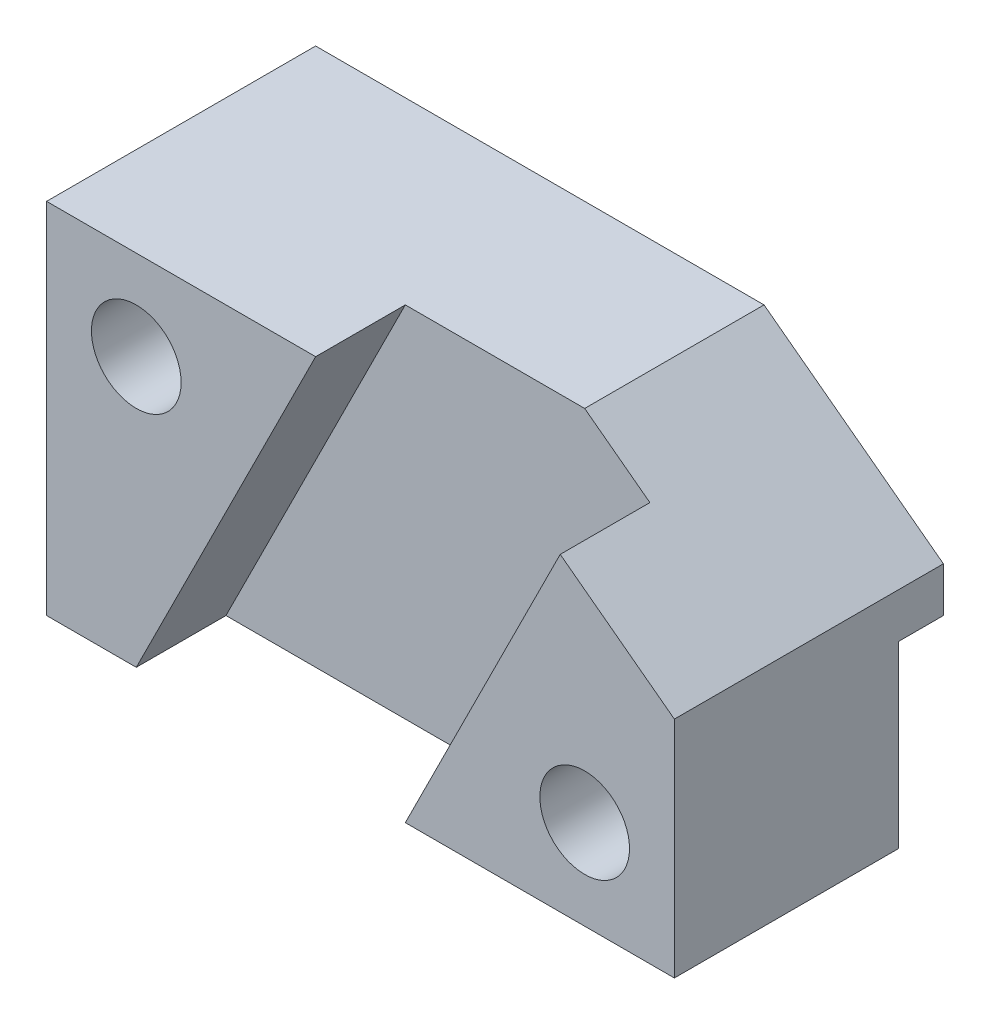
SolidWorks part; units mm, degrees
ref_plane "Front Plane" through (0, 0, 0) normal (0, 0, 1) x (1, 0, 0)
ref_plane "Top Plane" through (0, 0, 0) normal (0, 1, 0) x (1, 0, 0)
ref_plane "Right Plane" through (0, 0, 0) normal (1, 0, 0) x (0, 0, -1)
sketch "Sketch1" plane through (0, 0, 0) normal (0, 1, 0) x (1, 0, 0)
  line L1 (0, 0) -> (70, 0)
  line L2 (0, 0) -> (0, 30)
  line L3 (0, 30) -> (70, 30)
  line L4 (70, 0) -> (70, 30)
  dimension "D1" = 70
  dimension "D2" = 30
extrude "Boss-Extrude1" add sketch "Sketch1" along normal blind 40
sketch "Sketch2" plane through (0, 0, 0) normal (0, 0, 1) x (1, 0, 0)
  line L0 (0, 40) -> (30, 40) construction
  line L1 (0, 40) -> (70, 40) construction
  line L2 (70, 0) -> (40, 0) construction
  line L3 (0, 0) -> (70, 0) construction
  line L4 (70, 40) -> (60, 40) construction
  line L5 (0, 0) -> (10, 0) construction
  line L6 (30, 40) -> (10, 0)
  line L7 (10, 0) -> (40, 0)
  line L8 (40, 0) -> (60, 40)
  line L9 (60, 40) -> (30, 40)
  dimension "D1" = 10
  dimension "D2" = 30
  dimension "D3" = 30
  dimension "D4" = 10
extrude "Cut-Extrude1" cut sketch "Sketch2" against normal blind 10
sketch "Sketch3" plane through (0, 0, -30) normal (0, 0, -1) x (-1, 0, 0)
  line L0 (-70, 40) -> (-70, 25)
  line L1 (-70, 40) -> (-70, 0) construction
  line L2 (-70, 25) -> (-50, 40)
  line L3 (-70, 40) -> (0, 40) construction
  line L4 (-50, 40) -> (-70, 40)
  dimension "D1" = 15
  dimension "D2" = 20
extrude "Cut-Extrude2" cut sketch "Sketch3" against normal through all and the other way through all
sketch "Sketch4" plane through (70, 0, 0) normal (1, 0, 0) x (0, 0, -1)
  line L1 (30, 0) -> (25, 0)
  line L2 (30, 0) -> (30, 20)
  line L3 (30, 20) -> (25, 20)
  line L4 (25, 0) -> (25, 20)
  dimension "D1" = 20
  dimension "D2" = 5
extrude "Cut-Extrude3" cut sketch "Sketch4" against normal through all
sketch "Sketch5" plane through (0, 0, 0) normal (0, 0, 1) x (1, 0, 0)
  line L0 (70, 0) -> (60, 0) construction
  line L1 (40, 0) -> (70, 0) construction
  line L2 (60, 0) -> (60, 10) construction
  circle A0 centre (60, 10) radius 5
  dimension "D1" = 10
  dimension "D2" = 10
extrude "Cut-Extrude4" cut sketch "Sketch5" against normal through all contours A0
sketch "Sketch6" plane through (0, 0, 0) normal (0, 0, 1) x (1, 0, 0)
  line L0 (0, 40) -> (0, 30) construction
  line L1 (0, 40) -> (0, 0) construction
  line L2 (0, 30) -> (10, 30) construction
  circle A0 centre (10, 30) radius 5
  dimension "D1" = 10
  dimension "D2" = 10
extrude "Cut-Extrude5" cut sketch "Sketch6" against normal through all
